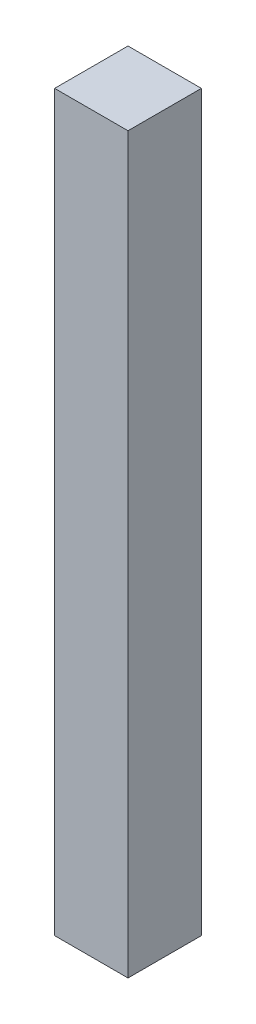
SolidWorks part; units mm, degrees
ref_plane "Front Plane" through (0, 0, 0) normal (0, 0, 1) x (1, 0, 0)
ref_plane "Top Plane" through (0, 0, 0) normal (0, 1, 0) x (1, 0, 0)
ref_plane "Right Plane" through (0, 0, 0) normal (1, 0, 0) x (0, 0, -1)
sketch "Sketch1" plane through (0, 0, 0) normal (0, 0, 1) x (1, 0, 0)
  line L1 (-5, -50) -> (5, -50)
  line L2 (-5, -50) -> (-5, 50)
  line L3 (-5, 50) -> (5, 50)
  line L4 (5, -50) -> (5, 50)
  line L5 (-5, -50) -> (5, 50) construction
  line L6 (-5, 50) -> (5, -50) construction
  point P0 (0, 0)
  dimension "D1" = 100
  dimension "D2" = 10
extrude "Boss-Extrude1" add sketch "Sketch1" along normal blind 10
